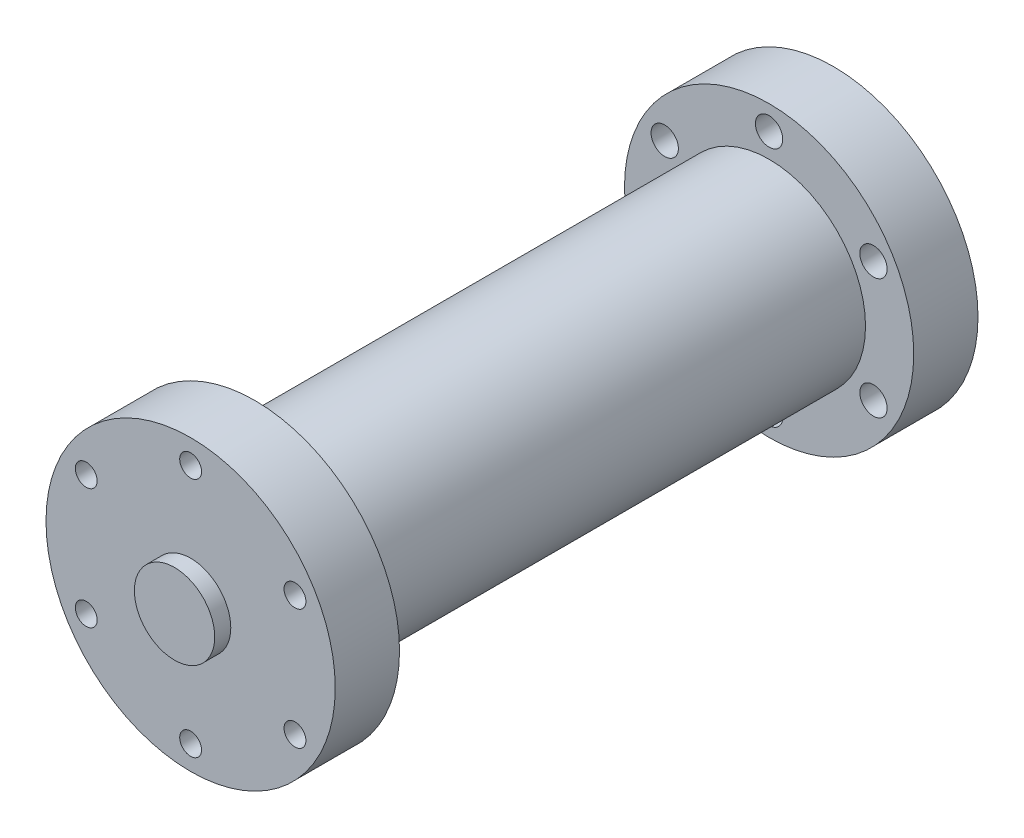
SolidWorks part; units mm, degrees
ref_plane "Plan de face" through (0, 0, 0) normal (0, 0, 1) x (1, 0, 0)
ref_plane "Plan de dessus" through (0, 0, 0) normal (0, 1, 0) x (1, 0, 0)
ref_plane "Plan de droite" through (0, 0, 0) normal (1, 0, 0) x (0, 0, -1)
sketch "Sketch1" plane through (0, 0, 0) normal (0, 0, 1) x (1, 0, 0)
  circle A0 centre (0, 0) radius 45
  dimension "D1" = 90
extrude "Boss-Extrude1" add sketch "Sketch1" along normal blind 20 contours A0
sketch "Sketch2" plane through (0, 0, 0) normal (0, 0, -1) x (-1, 0, 0)
  circle A0 centre (0, 0) radius 30
  dimension "D1" = 60
extrude "Boss-Extrude2" add sketch "Sketch2" along normal blind 160
sketch "Sketch3" plane through (0, 0, -160) normal (0, 0, -1) x (-1, 0, 0)
  circle A0 centre (0, 0) radius 45
  dimension "D1" = 90
extrude "Boss-Extrude3" add sketch "Sketch3" along normal blind 20
sketch "Sketch4" plane through (0, 0, 20) normal (0, 0, 1) x (1, 0, 0)
  circle A0 centre (0, 0) radius 12.5
  dimension "D1" = 25
extrude "Boss-Extrude4" add sketch "Sketch4" along normal blind 5
sketch "Sketch5" plane through (0, 0, 20) normal (0, 0, 1) x (1, 0, 0)
  circle A0 centre (0, 0) radius 37.5 construction
  dimension "D1" = 75
hole_wizard "M8x1.25 Tapped Hole1" positions "Sketch6" profile "Sketch7" tap size "M8x1.25" standard "ANSI Metric"
sketch "Sketch6" plane through (0, 0, 20) normal (0, 0, 1) x (1, 0, 0)
  circle A0 centre (0, 0) radius 37.5 construction
  point P0 (0, 37.5)
sketch "Sketch7" plane through (0, 37.5, 20) normal (1, 0, 0) x (0, -1, 0)
  line L0 (0, 0) -> (0, 200)
  line L1 (0, 200) -> (3.4, 200)
  line L2 (3.4, 200) -> (3.4, 0)
  line L5 (3.4, 0) -> (0, 0)
  line L11 (0, -6.35) -> (0, 107.95) construction
  dimension "Thread Major Dia." = 6.8
  dimension "Thru Tap Drill Depth" = 200
pattern_circular "CirPattern1" count 6 over 360 about axis through (0, 0, 0) along (0, 0, 1) of "M8x1.25 Tapped Hole1"
sketch "Sketch8" plane through (0, 0, -180) normal (0, 0, -1) x (-1, 0, 0)
  circle A0 centre (0, 0) radius 37.5 construction
  dimension "D1" = 75
hole_wizard "Ø8.5 (8.5) Diameter Hole1" positions "Sketch9" profile "Sketch10" hole size "Ø8.5" standard "ANSI Metric" end condition up to next
sketch "Sketch9" plane through (0, 0, -180) normal (0, 0, -1) x (-1, 0, 0)
  circle A0 centre (0, 0) radius 37.5 construction
  point P0 (0, 37.5)
sketch "Sketch10" plane through (0, 37.5, -180) normal (1, 0, 0) x (0, 1, 0)
  line L0 (0, 0) -> (0, 20.001)
  line L1 (0, 20.001) -> (4.25, 20.001)
  line L2 (4.25, 20.001) -> (4.25, 0)
  line L5 (4.25, 0) -> (0, 0)
  line L11 (0, -6.35) -> (0, 107.95) construction
  dimension "Thru Hole Dia." = 8.5
  dimension "Thru Hole Depth" = 20.001
pattern_circular "CirPattern2" count 6 over 360 about axis through (0, 0, 0) along (0, 0, 1) of "Ø8.5 (8.5) Diameter Hole1"
sketch "Sketch11" plane through (0, 0, -180) normal (0, 0, -1) x (-1, 0, 0)
  circle A0 centre (0, 0) radius 12.5
  dimension "D1" = 25
extrude "Cut-Extrude1" cut sketch "Sketch11" against normal blind 20
